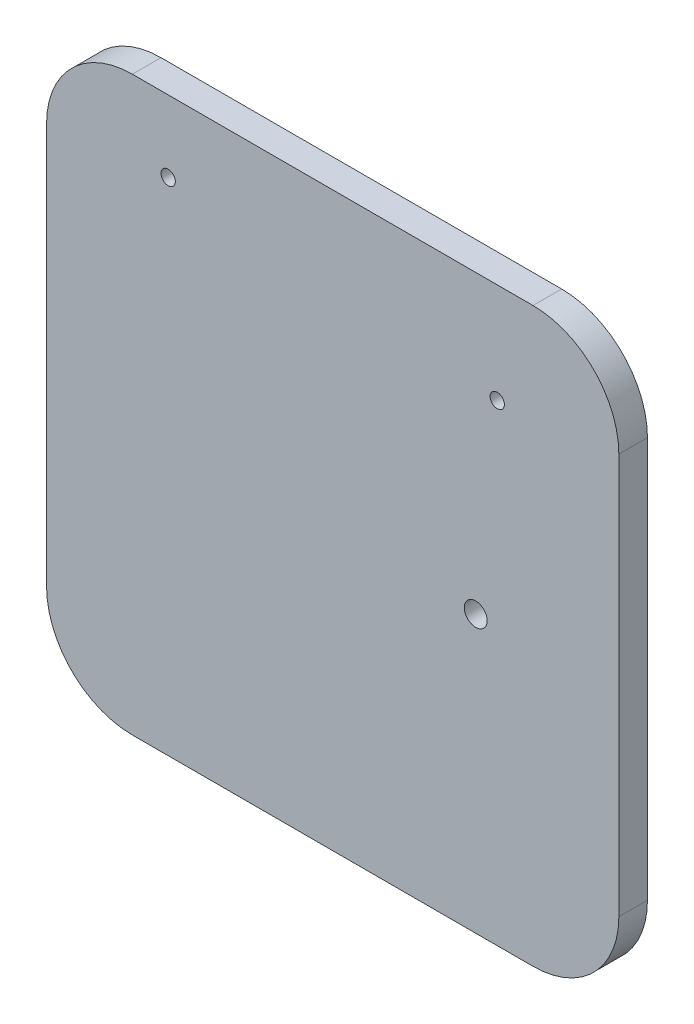
SolidWorks part; units mm, degrees
material "Mahogany"
ref_plane "Front Plane" through (0, 0, 0) normal (0, 0, 1) x (1, 0, 0)
ref_plane "Top Plane" through (0, 0, 0) normal (0, 1, 0) x (1, 0, 0)
ref_plane "Right Plane" through (0, 0, 0) normal (1, 0, 0) x (0, 0, -1)
sketch "Sketch1" plane through (0, 0, 0) normal (0, 0, 1) x (1, 0, 0)
  line L1 (-70, -100) -> (70, -100)
  line L2 (-100, -70) -> (-100, 70)
  line L3 (-70, 100) -> (70, 100)
  line L4 (100, -70) -> (100, 70)
  line L5 (-100, -100) -> (100, 100) construction
  line L6 (-100, 100) -> (100, -100) construction
  arc A0 (-70, -100) -> (-100, -70) centre (-70, -70) cw
  arc A1 (70, -100) -> (100, -70) centre (70, -70) ccw
  arc A2 (70, 100) -> (100, 70) centre (70, 70) cw
  arc A3 (-100, 70) -> (-70, 100) centre (-70, 70) cw
  circle A4 centre (49.983, -3.4294) radius 4
  point P0 (0, 0)
  dimension "D3" = 30
  dimension "D1" = 200
  dimension "D2" = 200
extrude "Boss-Extrude1" add sketch "Sketch1" along normal blind 10
sketch "Sketch2" plane through (0, 0, 10) normal (0, 0, 1) x (1, 0, 0)
  line L0 (0, 100) -> (0, -100) construction
  line L1 (70, 100) -> (-70, 100) construction
  line L2 (-70, -100) -> (70, -100) construction
  line L3 (57.5, 100) -> (57.5, 9.6778) construction
  circle A0 centre (-57.5, 75) radius 2.5
  circle A1 centre (57.5, 65) radius 2.5
  dimension "D1" = 5
  dimension "D4" = 5
  dimension "D2" = 25
  dimension "D3" = 57.5
  dimension "D5" = 35
extrude "Cut-Extrude1" cut sketch "Sketch2" against normal blind 10 and the other way through all
